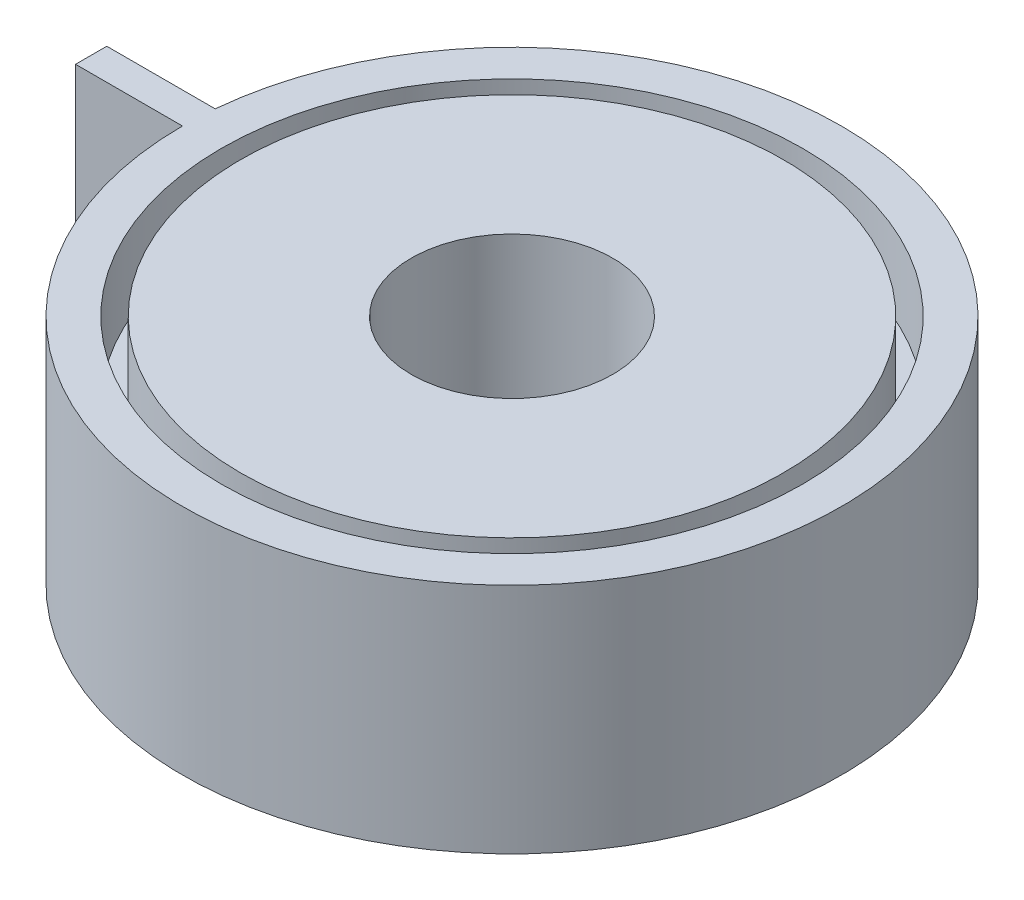
SolidWorks part; units mm, degrees
ref_plane "Front Plane" through (0, 0, 0) normal (0, 0, 1) x (1, 0, 0)
ref_plane "Top Plane" through (0, 0, 0) normal (0, 1, 0) x (1, 0, 0)
ref_plane "Right Plane" through (0, 0, 0) normal (1, 0, 0) x (0, 0, -1)
sketch "Sketch1" plane through (0, 0, 0) normal (0, 1, 0) x (1, 0, 0)
  line L0 (-85, 0) -> (-112.58, 0)
  line L1 (-112.58, 0) -> (-112.58, 8.0593)
  line L2 (-112.58, 8.0593) -> (-84.6171, 8.0593)
  arc A0 (-85, 0) -> (-84.6171, 8.0593) centre (0, 0) ccw
  circle A1 centre (0, 0) radius 26
extrude "Boss-Extrude1" add sketch "Sketch1" along normal blind 60
sketch "Sketch2" plane through (0, 0, 0) normal (0, -1, 0) x (-1, 0, 0)
  circle A0 centre (0, 0) radius 75
  circle A1 centre (0, 0) radius 70
extrude "Cut-Extrude1" cut sketch "Sketch2" against normal blind 20 contours A1 | A0
sketch "Sketch3" plane through (0, 60, 0) normal (0, 1, 0) x (1, 0, 0)
  circle A0 centre (0, 0) radius 75
  circle A1 centre (0, 0) radius 70
extrude "Cut-Extrude2" cut sketch "Sketch3" against normal blind 20
